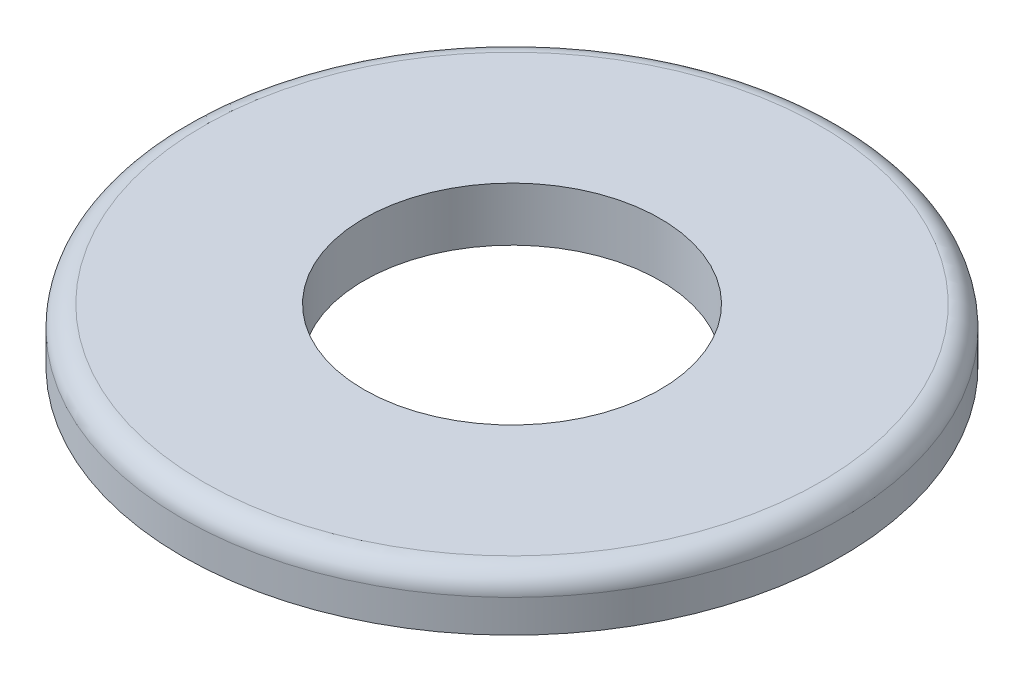
SolidWorks part; units mm, degrees
material "Alloy Steel"
ref_plane "Front Plane" through (0, 0, 0) normal (0, 0, 1) x (1, 0, 0)
ref_plane "Top Plane" through (0, 0, 0) normal (0, 1, 0) x (1, 0, 0)
ref_plane "Right Plane" through (0, 0, 0) normal (1, 0, 0) x (0, 0, -1)
sketch "Sketch1" plane through (0, 0, 0) normal (0, 1, 0) x (1, 0, 0)
  circle A0 centre (0, 0) radius 3.5687
  circle A1 centre (0, 0) radius 7.9375
  dimension "ID" = 7.1374
  dimension "OD" = 15.875
sketch "Sketch2" plane through (0, 0, 0) normal (1, 0, 0) x (0, 0, -1)
  line L1 (-7.9375, 0.6477) -> (7.9375, 0.6477)
  line L2 (-7.9375, 0.6477) -> (-7.9375, -0.6477)
  line L3 (-7.9375, -0.6477) -> (7.9375, -0.6477)
  line L4 (7.9375, 0.6477) -> (7.9375, -0.6477)
  line L5 (-7.9375, 0.6477) -> (7.9375, -0.6477) construction
  line L6 (-7.9375, -0.6477) -> (7.9375, 0.6477) construction
  point P0 (0, 0)
  point P6 (7.9375, 0)
  point P7 (-7.9375, 0)
  dimension "Thickness Range [Min]" = 1.2954
sketch "Sketch3" plane through (0, 0, 0) normal (0, 1, 0) x (1, 0, 0)
  circle A0 centre (0, 0) radius 7.9375
  circle A1 centre (0, 0) radius 3.5687
  circle A2 centre (0, 0) radius 7.9375 construction
  circle A3 centre (0, 0) radius 3.5687 construction
extrude "Boss-Extrude1" add sketch "Sketch3" along normal up to vertex (0.6477 mm away) and the other way up to vertex (0.6477 mm away) up to point (0, 0.6477, -7.9375) other way up to point (0, -0.6477, -7.9375)
fillet "Fillet1" radius 0.508 1 edges at (0, 0.6477, 7.9375)
